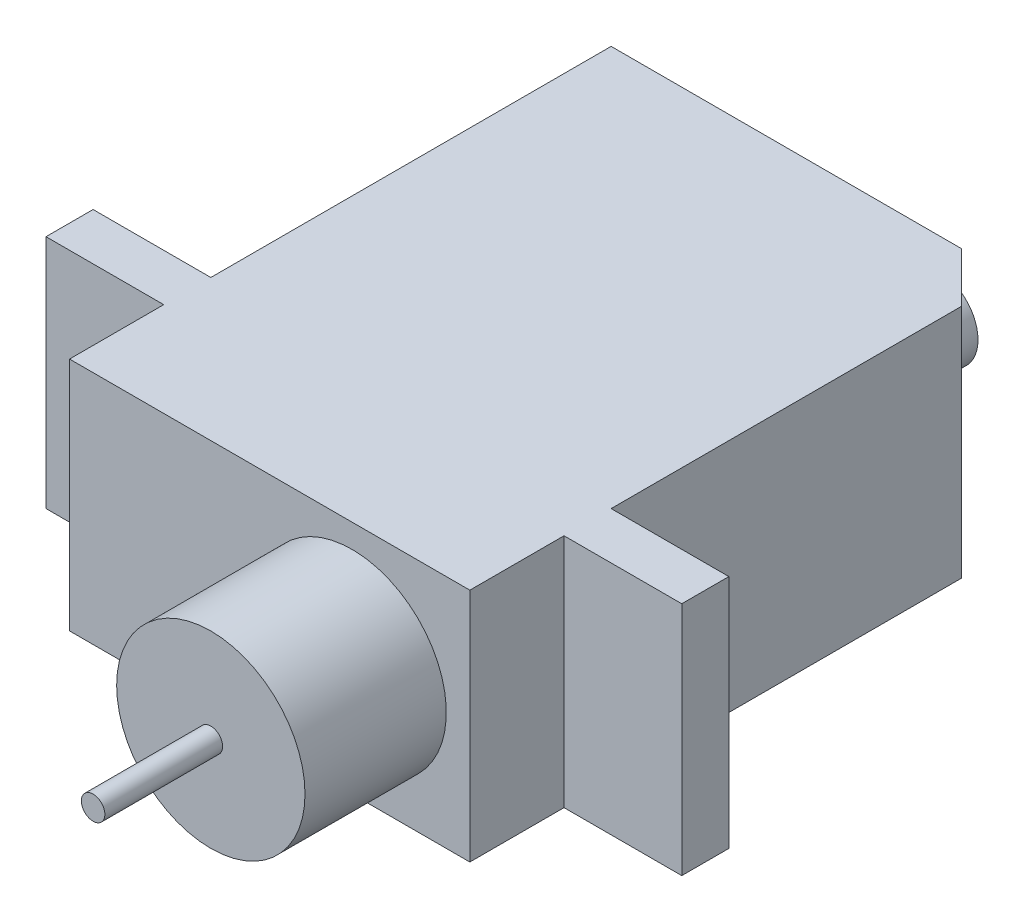
SolidWorks part; units mm, degrees
ref_plane "Front Plane" through (0, 0, 0) normal (0, 0, 1) x (1, 0, 0)
ref_plane "Top Plane" through (0, 0, 0) normal (0, 1, 0) x (1, 0, 0)
ref_plane "Right Plane" through (0, 0, 0) normal (1, 0, 0) x (0, 0, -1)
sketch "Sketch1" plane through (0, 0, 0) normal (0, 1, 0) x (1, 0, 0)
  line L0 (0, 0) -> (14.8787, 0)
  line L1 (14.8787, 0) -> (17, -2.1213)
  line L2 (17, -2.1213) -> (17, -17)
  line L3 (17, -17) -> (22, -17)
  line L4 (22, -17) -> (22, -19)
  line L5 (22, -19) -> (17, -19)
  line L6 (17, -19) -> (17, -23)
  line L7 (17, -23) -> (0, -23)
  line L8 (0, -23) -> (0, -19)
  line L9 (0, -19) -> (-5, -19)
  line L10 (-5, -19) -> (-5, -17)
  line L11 (-5, -17) -> (0, -17)
  line L12 (0, -17) -> (0, 0)
  dimension "D1" = 17
  dimension "D2" = 135
  dimension "D3" = 3
  dimension "D4" = 5
  dimension "D5" = 2
  dimension "D6" = 23
  dimension "D7" = 4
extrude "Boss-Extrude1" add sketch "Sketch1" along normal blind 10
sketch "Sketch2" plane through (0, 0, 23) normal (0, 0, 1) x (1, 0, 0)
  line L0 (17, 10) -> (17, 0) construction
  line L1 (0, 10) -> (17, 10) construction
  circle A0 centre (12, 5) radius 4
  dimension "D1" = 8
  dimension "D2" = 5
  dimension "D3" = 5
extrude "Boss-Extrude2" add sketch "Sketch2" along normal blind 6
sketch "Sketch3" plane through (0, 0, 29) normal (0, 0, 1) x (1, 0, 0)
  circle A0 centre (12, 5) radius 0.5
  dimension "D1" = 1
extrude "Boss-Extrude3" add sketch "Sketch3" along normal blind 5
sketch "Sketch4" plane through (0, 0, 0) normal (0, 0, -1) x (-1, 0, 0)
  line L0 (-14.8787, 0) -> (0, 0) construction
  line L1 (-14.8787, 10) -> (-14.8787, 0) construction
  circle A0 centre (-11.8787, 5) radius 1.7019
  dimension "D1" = 5
  dimension "D2" = 3
extrude "Boss-Extrude4" add sketch "Sketch4" along normal blind 2
